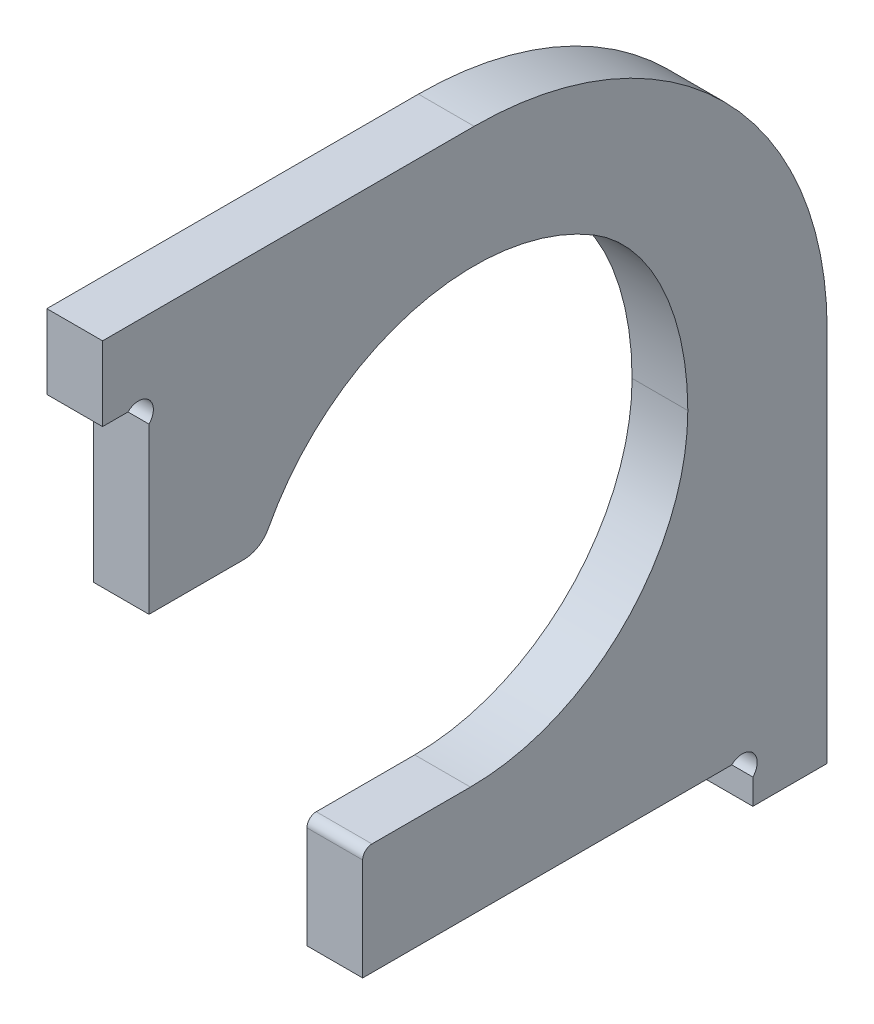
SolidWorks part; units mm, degrees
ref_plane "Plan de face" through (0, 0, 0) normal (0, 0, 1) x (1, 0, 0)
ref_plane "Plan de dessus" through (0, 0, 0) normal (0, 1, 0) x (1, 0, 0)
ref_plane "Plan de droite" through (0, 0, 0) normal (1, 0, 0) x (0, 0, -1)
sketch "Esquisse1" plane through (0, 0, 0) normal (1, 0, 0) x (0, 0, -1)
  line L0 (71, -14.0981) -> (71, 13.4131) construction
  line L1 (94.833, 1) -> (66.6987, 1) construction
  line L2 (-24.3695, 6) -> (94.833, 6) construction
  line L3 (6, -26.2376) -> (6, 112.02) construction
  line L4 (54, -14.0981) -> (54, 37.9301) construction
  line L5 (-4.9828, 51.4) -> (26.5452, 51.4) construction
  line L6 (41, 99.8569) -> (41, -16.9546) construction
  line L7 (65.2447, 41.4) -> (32.7277, 41.4) construction
  line L8 (40.6, 18) -> (30, 18)
  line L9 (1, 71.4) -> (3.7373, 71.4)
  line L10 (71, 6) -> (61.5299, -3.4701) construction
  line L11 (6, 71.4) -> (-10.0606, 55.3394) construction
  line L12 (79, -31.5309) -> (79, 70.0897) construction
  line L13 (-4.9828, 75.4) -> (32.7277, 75.4) construction
  line L14 (64, -14.0981) -> (64, 92.7701) construction
  line L15 (64, 30.5257) -> (74.5343, 41.06) construction
  line L16 (70.124, 45.1349) -> (64, 39.0109) construction
  line L17 (-4.9828, 61.4) -> (32.7277, 61.4) construction
  line L18 (6, 51.4) -> (16.2008, 51.4)
  line L19 (71, 3.7373) -> (71, 1)
  line L20 (29, -31.5309) -> (29, 32.8605) construction
  line L21 (94.833, 18) -> (10.3223, 18) construction
  line L22 (29, 17) -> (29, 6)
  line L25 (29, 6) -> (68.7373, 6)
  line L29 (6, 51.4) -> (6, 69.1373)
  line L30 (1, 104.5511) -> (1, 68.4) construction
  line L31 (61.8009, 79.4) -> (-8.9796, 79.4) construction
  line L32 (79, 41.4) -> (79, 1)
  line L33 (41, 79.4) -> (1, 79.4)
  line L34 (1, 79.4) -> (1, 71.4)
  line L35 (71, 1) -> (79, 1)
  arc A0 (30, 18) -> (29, 17) centre (30, 17) ccw
  arc A1 (71, 3.7373) -> (68.7373, 6) centre (69.8686, 4.8686) ccw
  arc A2 (6, 69.1373) -> (3.7373, 71.4) centre (4.8686, 70.2686) ccw
  arc A3 (53.8368, 62.8526) -> (18.8579, 53.0071) centre (41, 41.4) ccw
  arc A4 (79, 41.4) -> (41, 79.4) centre (41, 41.4) ccw
  arc A5 (16.2008, 51.4) -> (18.8579, 53.0071) centre (16.2008, 54.4) ccw
  arc A6 (40.6, 18) -> (64, 41.4) centre (40.6, 41.4) ccw
  ellipse E0 centre (47.1836, 41.4) end of major axis (47.1836, 18.0415) minor radius 16.8164 (64, 41.4) -> (53.8368, 62.8526) ccw
  point P60 (18.0871, 51.4)
  point P71 (29, 18)
  dimension "D7" = 10
  dimension "D12" = 6
  dimension "D14" = 12
  dimension "D13" = 50
  dimension "D3" = 8
  dimension "D5" = 15
  dimension "D9" = 5
  dimension "D4" = 45
  dimension "D10" = 1
  dimension "D11" = 3
  dimension "D1" = 4
  dimension "D2" = 5
  dimension "D6" = 14
  dimension "D8" = 10
extrude "Boss.-Extru.1" add sketch "Esquisse1" along normal blind 6
